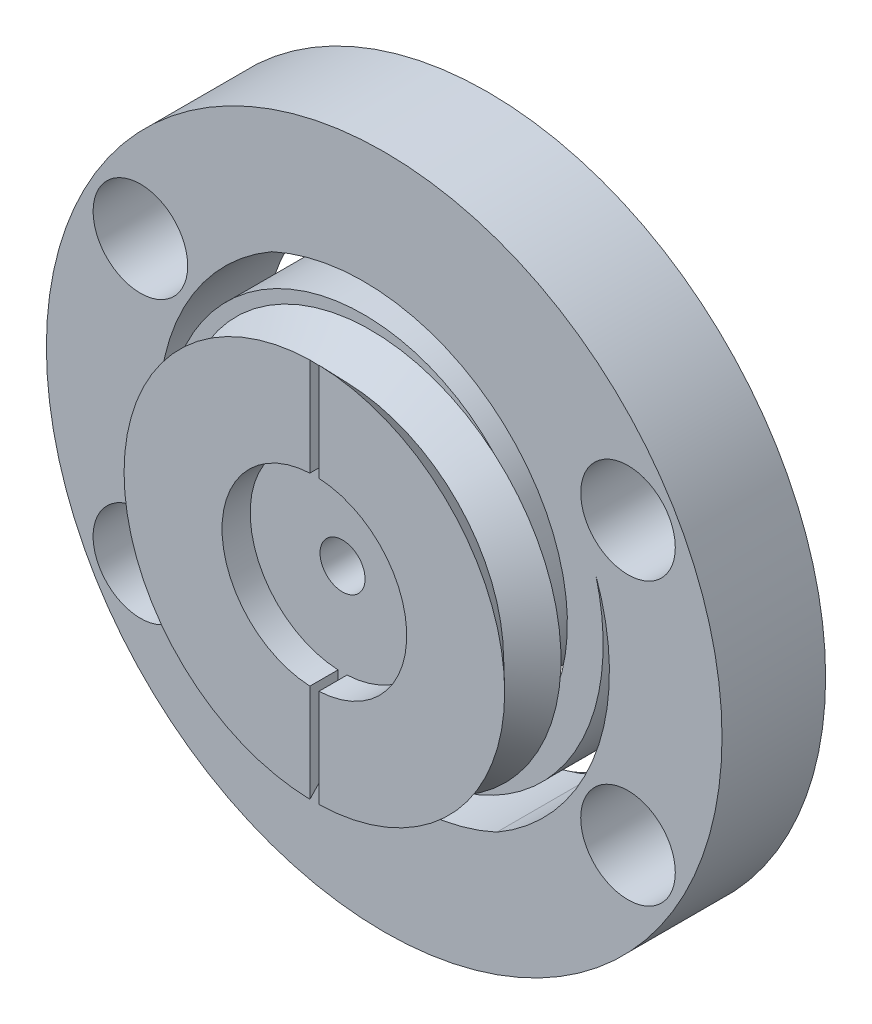
SolidWorks part; units mm, degrees
ref_plane "정면" through (0, 0, 0) normal (0, 0, 1) x (1, 0, 0)
ref_plane "윗면" through (0, 0, 0) normal (0, 1, 0) x (1, 0, 0)
ref_plane "우측면" through (0, 0, 0) normal (1, 0, 0) x (0, 0, -1)
sketch "스케치2" plane through (0, 0, 0) normal (0, 0, 1) x (1, 0, 0)
  circle A0 centre (0, 0) radius 15
  circle A1 centre (0, 0) radius 10
  point P13 (4.2374, 0.9394)
  dimension "D1" = 30
  dimension "D2" = 20
extrude "보스-돌출2" add sketch "스케치2" along normal blind 4.6
sketch "스케치23" plane through (0, 0, 4.6) normal (0, 0, 1) x (1, 0, 0)
  line L0 (0, 0) -> (10.8253, 6.25) construction
  line L1 (0, 0) -> (0, 15) construction
  line L2 (0, 0) -> (15, 0) construction
  circle A0 centre (10.8253, 6.25) radius 2.1
  circle A1 centre (0, 0) radius 15 construction
  circle A2 centre (-10.8253, 6.25) radius 2.1
  circle A3 centre (10.8253, -6.25) radius 2.1
  circle A4 centre (-10.8253, -6.25) radius 2.1
  dimension "D1" = 4.2
  dimension "D2" = 12.5
  dimension "D3" = 60
extrude "컷-돌출8" cut sketch "스케치23" against normal offset from surface (3.1 mm away) 1.5 up to face at (15, 0, 0)
sketch "스케치24" plane through (0, 0, 1.5) normal (0, 0, 1) x (1, 0, 0)
  circle A0 centre (-10.8253, 6.25) radius 1.2
  circle A1 centre (10.8253, 6.25) radius 1.2
  circle A2 centre (10.8253, -6.25) radius 1.2
  circle A3 centre (-10.8253, -6.25) radius 1.2
  dimension "D1" = 2.4
extrude "컷-돌출9" cut sketch "스케치24" against normal through all
sketch "스케치3" plane through (0, 0, 4.6) normal (0, 0, 1) x (1, 0, 0)
  circle A0 centre (0, 0) radius 10
  dimension "D1" = 20
curve "나선형 곡선1"
sketch "스케치4" plane through (0, 0, 4.6) normal (0, 0, 1) x (1, 0, 0)
  circle A0 centre (0, 0) radius 10
  dimension "D1" = 20
curve "나선형 곡선2"
sketch "스케치5" plane through (0, 0, 4.6) normal (0, 0, 1) x (1, 0, 0)
  circle A0 centre (0, 0) radius 10
  dimension "D1" = 20
curve "나선형 곡선3"
sketch "스케치6" plane through (0, 0, 4.6) normal (0, 0, 1) x (1, 0, 0)
  circle A0 centre (0, 0) radius 10
  dimension "D1" = 20
curve "나선형 곡선4"
sketch "스케치8" plane through (0, 0, 4.6) normal (0, 0, 1) x (1, 0, 0)
  arc A0 (-2.125, 3.6806) -> (-3.9937, -1.4536) centre (0, 0) ccw
  arc A1 (2.125, -3.6806) -> (3.9937, 1.4536) centre (0, 0) ccw
  arc A2 (-9.3969, -3.4202) -> (5, -8.6603) centre (0, 0) ccw
  arc A3 (9.3969, 3.4202) -> (-5, 8.6603) centre (0, 0) ccw
  spline S0 degree 3 poles (-1935.5381, 448.3535) (81.1193, 182.5863) (35.7886, -8.3056) (-0.0084, -9.6041) (-1.2597, -9.3952) (-3.5447, -8.5348) (-4.5777, -7.8842) (-6.2849, -6.2722) (-6.9587, -5.3118) (-7.872, -3.2507) (-8.1116, -2.151) (-8.1543, 0.0095) (-7.9579, 1.0694) (-7.195, 2.9909) (-6.6292, 3.8519) (-5.2463, 5.2605) (-4.4301, 5.8078) (-2.6949, 6.533) (-1.7768, 6.7109) (0.0106, 6.7046) (0.8791, 6.5207) (2.4371, 5.8552) (3.1261, 5.3742) (4.2361, 4.2204) (4.657, 3.5484) (5.194, 2.1391) (5.3103, 1.4026) (5.2548, -0.0117) (5.0835, -0.6888) (4.5154, -1.8832) (4.1192, -2.4003) (-12.3561, -16.8592) (-106.9283, 102.6405) (1865.2864, 715.7147) knots -1.641124 -1.641124 -1.641124 -1.641124 0.0625 0.0625 0.125 0.125 0.1875 0.1875 0.25 0.25 0.3125 0.3125 0.375 0.375 0.4375 0.4375 0.5 0.5 0.5625 0.5625 0.625 0.625 0.6875 0.6875 0.75 0.75 0.8125 0.8125 0.875 0.875 0.9375 0.9375 3.102152 3.102152 3.102152 3.102152 only from (5, -8.6603) to (2.125, -3.6806) construction
  spline S1 degree 3 poles (777.6447, 1828.2772) (165.7262, -111.5927) (-14.3941, -33.8027) (-9.4567, 1.676) (-9.0337, 2.872) (-7.7897, 4.9729) (-6.9695, 5.8772) (-5.0856, 7.2786) (-4.0228, 7.7753) (-1.8343, 8.3169) (-0.7097, 8.3618) (1.4254, 8.0288) (2.435, 7.6513) (4.1948, 6.5664) (4.9445, 5.8596) (6.0916, 4.2531) (6.4889, 3.3543) (6.9017, 1.5195) (6.9175, 0.5844) (6.6009, -1.1747) (6.269, -1.998) (5.3431, -3.4168) (4.7497, -4.0118) (3.4207, -4.9047) (2.6858, -5.2024) (1.2047, -5.4866) (0.4592, -5.4732) (-0.924, -5.173) (-1.561, -4.8867) (-2.6387, -4.1198) (-3.0791, -3.6398) (-14.4575, 15.096) (119.6491, 87.4805) (380.9378, -1961.2311) knots -1.641124 -1.641124 -1.641124 -1.641124 0.0625 0.0625 0.125 0.125 0.1875 0.1875 0.25 0.25 0.3125 0.3125 0.375 0.375 0.4375 0.4375 0.5 0.5 0.5625 0.5625 0.625 0.625 0.6875 0.6875 0.75 0.75 0.8125 0.8125 0.875 0.875 0.9375 0.9375 3.102152 3.102152 3.102152 3.102152 only from (-9.3969, -3.4202) to (-3.9937, -1.4536) construction
  spline S2 degree 3 poles (-777.6447, -1828.2772) (-165.7262, 111.5927) (14.3941, 33.8027) (9.4567, -1.676) (9.0337, -2.872) (7.7897, -4.9729) (6.9695, -5.8772) (5.0856, -7.2786) (4.0228, -7.7753) (1.8343, -8.3169) (0.7097, -8.3618) (-1.4254, -8.0288) (-2.435, -7.6513) (-4.1948, -6.5664) (-4.9445, -5.8596) (-6.0916, -4.2531) (-6.4889, -3.3543) (-6.9017, -1.5195) (-6.9175, -0.5844) (-6.6009, 1.1747) (-6.269, 1.998) (-5.3431, 3.4168) (-4.7497, 4.0118) (-3.4207, 4.9047) (-2.6858, 5.2024) (-1.2047, 5.4866) (-0.4592, 5.4732) (0.924, 5.173) (1.561, 4.8867) (2.6387, 4.1198) (3.0791, 3.6398) (14.4575, -15.096) (-119.6491, -87.4805) (-380.9378, 1961.2311) knots -1.641124 -1.641124 -1.641124 -1.641124 0.0625 0.0625 0.125 0.125 0.1875 0.1875 0.25 0.25 0.3125 0.3125 0.375 0.375 0.4375 0.4375 0.5 0.5 0.5625 0.5625 0.625 0.625 0.6875 0.6875 0.75 0.75 0.8125 0.8125 0.875 0.875 0.9375 0.9375 3.102152 3.102152 3.102152 3.102152 only from (9.3969, 3.4202) to (3.9937, 1.4536) construction
  spline S3 degree 3 poles (1935.5381, -448.3535) (-81.1193, -182.5863) (-35.7886, 8.3056) (0.0084, 9.6041) (1.2597, 9.3952) (3.5447, 8.5348) (4.5777, 7.8842) (6.2849, 6.2722) (6.9587, 5.3118) (7.872, 3.2507) (8.1116, 2.151) (8.1543, -0.0095) (7.9579, -1.0694) (7.195, -2.9909) (6.6292, -3.8519) (5.2463, -5.2605) (4.4301, -5.8078) (2.6949, -6.533) (1.7768, -6.7109) (-0.0106, -6.7046) (-0.8791, -6.5207) (-2.4371, -5.8552) (-3.1261, -5.3742) (-4.2361, -4.2204) (-4.657, -3.5484) (-5.194, -2.1391) (-5.3103, -1.4026) (-5.2548, 0.0117) (-5.0835, 0.6888) (-4.5154, 1.8832) (-4.1192, 2.4003) (12.3561, 16.8592) (106.9283, -102.6405) (-1865.2864, -715.7147) knots -1.641124 -1.641124 -1.641124 -1.641124 0.0625 0.0625 0.125 0.125 0.1875 0.1875 0.25 0.25 0.3125 0.3125 0.375 0.375 0.4375 0.4375 0.5 0.5 0.5625 0.5625 0.625 0.625 0.6875 0.6875 0.75 0.75 0.8125 0.8125 0.875 0.875 0.9375 0.9375 3.102152 3.102152 3.102152 3.102152 only from (-5, 8.6603) to (-2.125, 3.6806) construction
  spline S4 degree 3 poles (5, -8.6603) (3.8065, -9.211) (2.5251, -9.5122) (-0.0084, -9.6041) (-1.2597, -9.3952) (-3.5447, -8.5348) (-4.5777, -7.8842) (-6.2849, -6.2722) (-6.9587, -5.3118) (-7.872, -3.2507) (-8.1116, -2.151) (-8.1543, 0.0095) (-7.9579, 1.0694) (-7.195, 2.9909) (-6.6292, 3.8519) (-5.2463, 5.2605) (-4.4301, 5.8078) (-2.6949, 6.533) (-1.7768, 6.7109) (0.0106, 6.7046) (0.8791, 6.5207) (2.4371, 5.8552) (3.1261, 5.3742) (4.2361, 4.2204) (4.657, 3.5484) (5.194, 2.1391) (5.3103, 1.4026) (5.2548, -0.0117) (5.0835, -0.6888) (4.5154, -1.8832) (4.1192, -2.4003) (3.1945, -3.2118) (2.6667, -3.5062) (2.125, -3.6806) knots 0 0 0 0 0.0625 0.0625 0.125 0.125 0.1875 0.1875 0.25 0.25 0.3125 0.3125 0.375 0.375 0.4375 0.4375 0.5 0.5 0.5625 0.5625 0.625 0.625 0.6875 0.6875 0.75 0.75 0.8125 0.8125 0.875 0.875 0.9375 0.9375 1 1 1 1
  spline S5 degree 3 poles (-9.3969, -3.4202) (-9.7321, -2.1492) (-9.8062, -0.835) (-9.4567, 1.676) (-9.0337, 2.872) (-7.7897, 4.9729) (-6.9695, 5.8772) (-5.0856, 7.2786) (-4.0228, 7.7753) (-1.8343, 8.3169) (-0.7097, 8.3618) (1.4254, 8.0288) (2.435, 7.6513) (4.1948, 6.5664) (4.9445, 5.8596) (6.0916, 4.2531) (6.4889, 3.3543) (6.9017, 1.5195) (6.9175, 0.5844) (6.6009, -1.1747) (6.269, -1.998) (5.3431, -3.4168) (4.7497, -4.0118) (3.4207, -4.9047) (2.6858, -5.2024) (1.2047, -5.4866) (0.4592, -5.4732) (-0.924, -5.173) (-1.561, -4.8867) (-2.6387, -4.1198) (-3.0791, -3.6398) (-3.7177, -2.5883) (-3.916, -2.0173) (-3.9937, -1.4536) knots 0 0 0 0 0.0625 0.0625 0.125 0.125 0.1875 0.1875 0.25 0.25 0.3125 0.3125 0.375 0.375 0.4375 0.4375 0.5 0.5 0.5625 0.5625 0.625 0.625 0.6875 0.6875 0.75 0.75 0.8125 0.8125 0.875 0.875 0.9375 0.9375 1 1 1 1
  spline S6 degree 3 poles (9.3969, 3.4202) (9.7321, 2.1492) (9.8062, 0.835) (9.4567, -1.676) (9.0337, -2.872) (7.7897, -4.9729) (6.9695, -5.8772) (5.0856, -7.2786) (4.0228, -7.7753) (1.8343, -8.3169) (0.7097, -8.3618) (-1.4254, -8.0288) (-2.435, -7.6513) (-4.1948, -6.5664) (-4.9445, -5.8596) (-6.0916, -4.2531) (-6.4889, -3.3543) (-6.9017, -1.5195) (-6.9175, -0.5844) (-6.6009, 1.1747) (-6.269, 1.998) (-5.3431, 3.4168) (-4.7497, 4.0118) (-3.4207, 4.9047) (-2.6858, 5.2024) (-1.2047, 5.4866) (-0.4592, 5.4732) (0.924, 5.173) (1.561, 4.8867) (2.6387, 4.1198) (3.0791, 3.6398) (3.7177, 2.5883) (3.916, 2.0173) (3.9937, 1.4536) knots 0 0 0 0 0.0625 0.0625 0.125 0.125 0.1875 0.1875 0.25 0.25 0.3125 0.3125 0.375 0.375 0.4375 0.4375 0.5 0.5 0.5625 0.5625 0.625 0.625 0.6875 0.6875 0.75 0.75 0.8125 0.8125 0.875 0.875 0.9375 0.9375 1 1 1 1
  spline S7 degree 3 poles (-5, 8.6603) (-3.8065, 9.211) (-2.5251, 9.5122) (0.0084, 9.6041) (1.2597, 9.3952) (3.5447, 8.5348) (4.5777, 7.8842) (6.2849, 6.2722) (6.9587, 5.3118) (7.872, 3.2507) (8.1116, 2.151) (8.1543, -0.0095) (7.9579, -1.0694) (7.195, -2.9909) (6.6292, -3.8519) (5.2463, -5.2605) (4.4301, -5.8078) (2.6949, -6.533) (1.7768, -6.7109) (-0.0106, -6.7046) (-0.8791, -6.5207) (-2.4371, -5.8552) (-3.1261, -5.3742) (-4.2361, -4.2204) (-4.657, -3.5484) (-5.194, -2.1391) (-5.3103, -1.4026) (-5.2548, 0.0117) (-5.0835, 0.6888) (-4.5154, 1.8832) (-4.1192, 2.4003) (-3.1945, 3.2118) (-2.6667, 3.5062) (-2.125, 3.6806) knots 0 0 0 0 0.0625 0.0625 0.125 0.125 0.1875 0.1875 0.25 0.25 0.3125 0.3125 0.375 0.375 0.4375 0.4375 0.5 0.5 0.5625 0.5625 0.625 0.625 0.6875 0.6875 0.75 0.75 0.8125 0.8125 0.875 0.875 0.9375 0.9375 1 1 1 1
extrude "보스-돌출3" add sketch "스케치8" against normal blind 4.4
sketch "스케치19" plane through (0, 0, 0.2) normal (0, 0, -1) x (-1, 0, 0)
  circle A0 centre (0, 0) radius 3.975
  dimension "D1" = 7.95
extrude "보스-돌출6" add sketch "스케치19" along normal blind 3.4
sketch "스케치9" plane through (0, 0, -3.2) normal (0, 0, -1) x (-1, 0, 0)
  circle A0 centre (0, 0) radius 3.1
  dimension "D1" = 6.2
extrude "컷-돌출1" cut sketch "스케치9" against normal blind 3.1
sketch "스케치10" plane through (0, 0, 4.6) normal (0, 0, 1) x (1, 0, 0)
  circle A0 centre (0, 0) radius 4
  dimension "D1" = 8
extrude "보스-돌출4" add sketch "스케치10" along normal blind 0.6
sketch "스케치11" plane through (0, 0, 5.2) normal (0, 0, 1) x (1, 0, 0)
  circle A0 centre (0, 0) radius 8.45
  point P14 (0, 0)
  dimension "D1" = 16.9
extrude "보스-돌출5" add sketch "스케치11" along normal blind 2.5
sketch "스케치12" plane through (0, 0, 0) normal (1, 0, 0) x (0, 0, -1)
  line L0 (0, 0) -> (-7.7, 0) construction
  line L1 (-7.7, 8.45) -> (-7.7, -8.45) construction
  line L2 (-7.7, 8.45) -> (-5.2, 8.45)
  line L3 (-5.2, 8.45) -> (-6.45, 7.15)
  line L4 (-6.45, 7.15) -> (-7.7, 8.45)
  point P11 (-6.45, 8.45)
  dimension "D1" = 1.3
revolve "컷-회전1" cut sketch "스케치12" angle 360 about L0
fillet "필렛1" [suppressed] radius 0.1
sketch "스케치25" plane through (0, 0, 7.7) normal (0, 0, 1) x (1, 0, 0)
  circle A0 centre (0, 0) radius 1
  dimension "D1" = 2
extrude "컷-돌출10" cut sketch "스케치25" against normal blind 7
sketch "스케치26" plane through (0, 0, 7.7) normal (0, 0, 1) x (1, 0, 0)
  line L0 (-0.2, 4.0951) -> (-0.2, 9)
  line L1 (-0.2, -9) -> (0.2, -9)
  line L2 (-0.2, -9) -> (-0.2, -4.0951)
  line L3 (-0.2, 9) -> (0.2, 9)
  line L4 (0.2, -9) -> (0.2, -4.0951)
  line L5 (-0.2, -9) -> (0.2, 9) construction
  line L6 (-0.2, 9) -> (0.2, -9) construction
  line L7 (0.2, 4.0951) -> (0.2, 9)
  arc A0 (-0.2, 4.0951) -> (-0.2, -4.0951) centre (0, 0) ccw
  arc A1 (0.2, -4.0951) -> (0.2, 4.0951) centre (0, 0) ccw
  point P0 (0, 0)
  dimension "D3" = 8.2
  dimension "D1" = 18
  dimension "D2" = 0.4
extrude "컷-돌출11" cut sketch "스케치26" against normal blind 1.25
